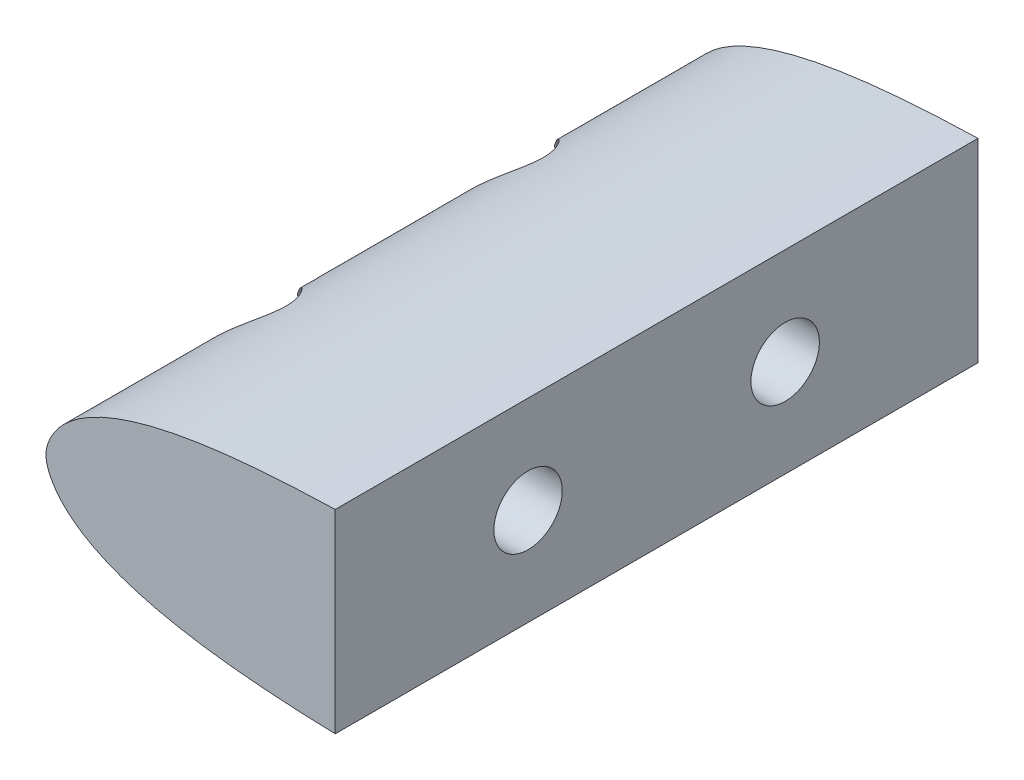
SolidWorks part; units mm, degrees
ref_plane "Front Plane" through (0, 0, 0) normal (0, 0, 1) x (1, 0, 0)
ref_plane "Top Plane" through (0, 0, 0) normal (0, 1, 0) x (1, 0, 0)
ref_plane "Right Plane" through (0, 0, 0) normal (1, 0, 0) x (0, 0, -1)
curve "Curve1"
  spline degree 3 poles (25.4, 0.032, 0) (24.9768, 0.0904, 0) (24.1307, 0.2071, 0) (22.8605, 0.3691, 0) (21.5905, 0.5229, 0) (20.3205, 0.6676, 0) (19.0504, 0.804, 0) (17.7804, 0.9321, 0) (16.5104, 1.0514, 0) (15.2404, 1.1606, 0) (13.9704, 1.2598, 0) (12.692, 1.3473, 0) (11.4135, 1.4221, 0) (10.1349, 1.4776, 0) (8.8649, 1.5185, 0) (7.8146, 1.5178, 0) (6.9766, 1.5373, 0) (6.35, 1.546, 0) (5.715, 1.5506, 0) (5.0799, 1.5478, 0) (4.4448, 1.5346, 0) (3.8095, 1.5078, 0) (3.1738, 1.462, 0) (2.5803, 1.3959, 0) (2.0289, 1.3055, 0) (1.6052, 1.2091, 0) (1.2675, 1.107, 0) (1.012, 1.0136, 0) (0.7549, 0.8965, 0) (0.4933, 0.743, 0) (0.2762, 0.5635, 0) (0.0851, 0.3233, 0) (-0.0556, 0, 0) (0.0851, -0.3233, 0) (0.2762, -0.5635, 0) (0.4933, -0.743, 0) (0.7549, -0.8965, 0) (1.012, -1.0136, 0) (1.2675, -1.107, 0) (1.6052, -1.2091, 0) (2.0289, -1.3055, 0) (2.5803, -1.3959, 0) (3.1738, -1.462, 0) (3.8095, -1.5078, 0) (4.4448, -1.5346, 0) (5.0799, -1.5478, 0) (5.715, -1.5506, 0) (6.35, -1.546, 0) (6.9766, -1.5373, 0) (7.8146, -1.5178, 0) (8.8649, -1.5185, 0) (10.1349, -1.4776, 0) (11.4135, -1.4221, 0) (12.692, -1.3473, 0) (13.9704, -1.2598, 0) (15.2404, -1.1606, 0) (16.5104, -1.0514, 0) (17.7804, -0.9321, 0) (19.0504, -0.804, 0) (20.3205, -0.6676, 0) (21.5905, -0.5229, 0) (22.8605, -0.3691, 0) (24.1307, -0.2071, 0) (24.9768, -0.0904, 0) (25.4, -0.032, 0) knots 0 0 0 0 0.024634 0.049243 0.07383 0.098397 0.122946 0.147479 0.171995 0.196494 0.220976 0.245442 0.27038 0.294813 0.319232 0.343642 0.35536 0.367566 0.379771 0.391975 0.404183 0.416399 0.428636 0.44092 0.450818 0.460843 0.465946 0.471149 0.476523 0.482208 0.488618 0.492568 0.5 0.507432 0.511382 0.517792 0.523477 0.528851 0.534054 0.539157 0.549182 0.55908 0.571364 0.583601 0.595817 0.608025 0.620229 0.632434 0.64464 0.656358 0.680768 0.705187 0.72962 0.754558 0.779024 0.803506 0.828005 0.852521 0.877054 0.901603 0.92617 0.950757 0.975366 1 1 1 1
sketch "Sketch2" plane through (0, 0, 0) normal (0, 0, 1) x (1, 0, 0)
  line L0 (28.575, 9.6007) -> (28.575, -9.6007)
  spline S1 degree 3 poles (28.575, 9.6007) (28.3104, 9.5935) (26.7222, 9.5469) (23.8091, 9.4239) (19.8365, 9.1376) (16.1269, 8.7246) (12.6805, 8.1595) (10.0325, 7.5569) (7.9221, 6.9188) (6.3248, 6.335) (4.7181, 5.603) (3.0829, 4.6438) (1.7265, 3.522) (0.5319, 2.0204) (-0.3474, 0) (0.5319, -2.0204) (1.7265, -3.522) (3.0829, -4.6438) (4.7181, -5.603) (6.3248, -6.335) (7.9221, -6.9188) (10.0325, -7.5569) (12.6805, -8.1595) (16.1269, -8.7246) (19.8365, -9.1376) (23.8091, -9.4239) (26.7222, -9.5469) (28.3104, -9.5935) (28.575, -9.6007) knots 0.401741 0.401741 0.401741 0.401741 0.404183 0.416399 0.428636 0.44092 0.450818 0.460843 0.465946 0.471149 0.476523 0.482208 0.488618 0.492568 0.5 0.507432 0.511382 0.517792 0.523477 0.528851 0.534054 0.539157 0.549182 0.55908 0.571364 0.583601 0.595817 0.598259 0.598259 0.598259 0.598259
  dimension "D1" = 28.575
extrude "Boss-Extrude1" add sketch "Sketch2" along normal blind 63.5
sketch "Sketch3" plane through (0, 0, 0) normal (1, 0, 0) x (0, 0, -1)
  line L0 (0, 0) -> (-63.5, 0) construction
  line L1 (-63.5, 9.6007) -> (-63.5, -9.6007) construction
hole_wizard "CBORE for 1/4 Socket Head Cap Screw1" positions "3DSketch2" profile "Sketch5" counterbore size "1/4" standard "ANSI Inch" end condition through all
sketch3d "3DSketch2"
  line L1 (0, 0, 0) -> (0, 0, 63.5) construction
  point P4 (0, 0, 19.05)
  point P13 (0, 0, 44.45)
  dimension "D1" = 25.4
  dimension "D2" = 19.05
sketch "Sketch5" plane through (0, 0, 19.05) normal (0, 1, 0) x (0, 0, 1)
  line L0 (0, 0) -> (0, 28.575)
  line L1 (0, 28.575) -> (3.3782, 28.575)
  line L3 (3.3782, 28.575) -> (3.3782, 6.35)
  line L4 (5.5562, 6.35) -> (3.3782, 6.35)
  line L5 (5.5562, 6.35) -> (5.5562, 0.5328)
  line L6 (5.5562, 0.5328) -> (6.1913, 0)
  line L7 (6.1913, 0) -> (0, 0)
  line L8 (-5.5562, 0.5328) -> (-6.1913, 0) construction
  line L11 (0, -6.35) -> (0, 107.95) construction
  dimension "Thru Hole Dia." = 6.7564
  dimension "Thru Hole Depth" = 28.575
  dimension "C'Bore Dia." = 11.1125
  dimension "C'Bore Depth" = 6.35
  dimension "Near C'Sink Dia." = 12.3825
  dimension "Near C'Sink Angle" = 100
